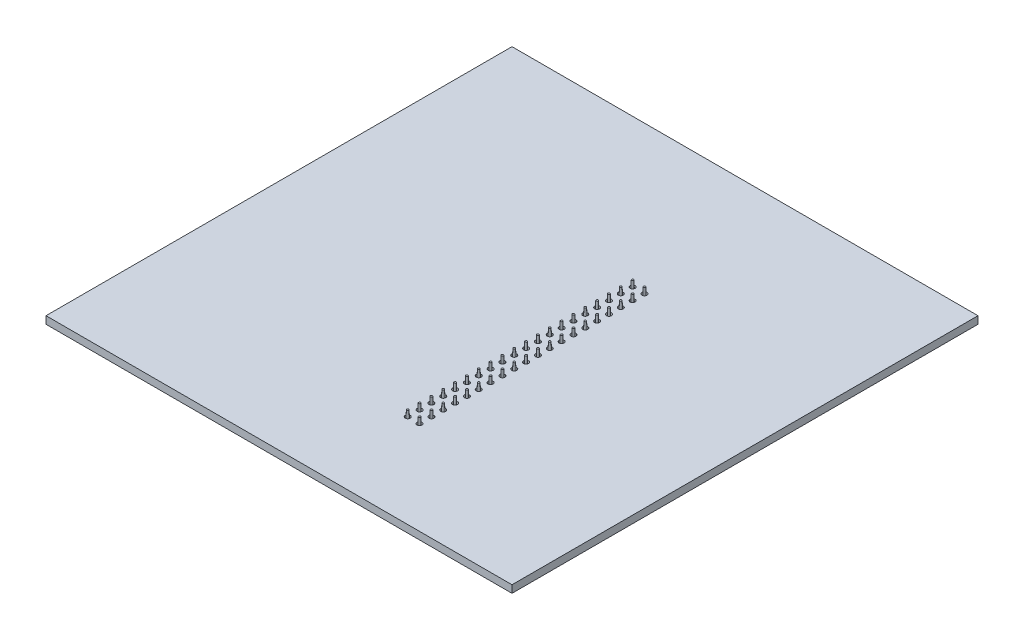
SolidWorks part; units mm, degrees
ref_plane "Front Plane" through (0, 0, 0) normal (0, 0, 1) x (1, 0, 0)
ref_plane "Top Plane" through (0, 0, 0) normal (0, 1, 0) x (1, 0, 0)
ref_plane "Right Plane" through (0, 0, 0) normal (1, 0, 0) x (0, 0, -1)
sketch "Sketch1" plane through (0, 0, 0) normal (0, 1, 0) x (1, 0, 0)
  line L1 (-50, -50) -> (50, -50)
  line L2 (-50, -50) -> (-50, 50)
  line L3 (-50, 50) -> (50, 50)
  line L4 (50, -50) -> (50, 50)
  line L5 (-50, -50) -> (50, 50) construction
  line L6 (-50, 50) -> (50, -50) construction
  point P0 (0, 0)
  dimension "D1" = 100
  dimension "D2" = 100
extrude "Boss-Extrude1" add sketch "Sketch1" along normal blind 1.6
sketch "Sketch2" plane through (0, 1.6, 0) normal (0, 1, 0) x (1, 0, 0)
  line L0 (10.138, -29.974) -> (10.138, -27.434) construction
  circle A0 centre (10.138, -29.974) radius 0.535
  circle A1 centre (7.598, -29.974) radius 0.535
  circle A2 centre (7.598, -27.434) radius 0.535
  circle A3 centre (7.598, -24.894) radius 0.535
  circle A4 centre (7.598, -22.354) radius 0.535
  circle A5 centre (7.598, -19.814) radius 0.535
  circle A6 centre (7.598, -17.274) radius 0.535
  circle A7 centre (7.598, -14.734) radius 0.535
  circle A8 centre (7.598, -12.194) radius 0.535
  circle A9 centre (7.598, -9.654) radius 0.535
  circle A10 centre (7.598, -7.114) radius 0.535
  circle A11 centre (7.598, -4.574) radius 0.535
  circle A12 centre (7.598, -2.034) radius 0.535
  circle A13 centre (7.598, 0.506) radius 0.535
  circle A14 centre (7.598, 3.046) radius 0.535
  circle A15 centre (7.598, 5.586) radius 0.535
  circle A16 centre (7.598, 8.126) radius 0.535
  circle A17 centre (7.598, 10.666) radius 0.535
  circle A18 centre (7.598, 13.206) radius 0.535
  circle A19 centre (7.598, 15.746) radius 0.535
  circle A20 centre (7.598, 18.286) radius 0.535
  circle A21 centre (10.138, -27.434) radius 0.535
  circle A22 centre (10.138, -24.894) radius 0.535
  circle A23 centre (10.138, -22.354) radius 0.535
  circle A24 centre (10.138, -19.814) radius 0.535
  circle A25 centre (10.138, -17.274) radius 0.535
  circle A26 centre (10.138, -14.734) radius 0.535
  circle A27 centre (10.138, -12.194) radius 0.535
  circle A28 centre (10.138, -9.654) radius 0.535
  circle A29 centre (10.138, -7.114) radius 0.535
  circle A30 centre (10.138, -4.574) radius 0.535
  circle A31 centre (10.138, -2.034) radius 0.535
  circle A32 centre (10.138, 0.506) radius 0.535
  circle A33 centre (10.138, 3.046) radius 0.535
  circle A34 centre (10.138, 5.586) radius 0.535
  circle A35 centre (10.138, 8.126) radius 0.535
  circle A36 centre (10.138, 10.666) radius 0.535
  circle A37 centre (10.138, 13.206) radius 0.535
  circle A38 centre (10.138, 15.746) radius 0.535
  circle A39 centre (10.138, 18.286) radius 0.535
  dimension "D1" = 1.07
  dimension "D2" = 39.862
  dimension "D3" = 20.026
  dimension "D6" = 2.54
  dimension "D4" = 2
  dimension "D5" = 20
extrude "Cut-Extrude1" cut sketch "Sketch2" against normal through all
ref_plane "Plane1" through (0, -9.4, 0) normal (0, -1, 0) x (-1, 0, 0)
sketch "Sketch4" plane through (0, -9.4, 0) normal (0, 1, 0) x (1, 0, 0)
  line L0 (9.368, -29.204) -> (10.908, -29.204)
  line L1 (8.868, -31.244) -> (11.408, -31.244)
  line L2 (8.868, -31.244) -> (8.868, -28.704)
  line L3 (8.868, -28.704) -> (11.408, -28.704)
  line L4 (11.408, -31.244) -> (11.408, -28.704)
  line L5 (8.868, -31.244) -> (11.408, -28.704) construction
  line L6 (8.868, -28.704) -> (11.408, -31.244) construction
  line L7 (10.908, -30.744) -> (10.908, -29.204)
  line L8 (9.368, -30.744) -> (10.908, -30.744)
  line L9 (9.368, -30.744) -> (9.368, -29.204)
  point P0 (10.138, -29.974)
  dimension "D1" = 2.54
  dimension "D2" = 2.54
  dimension "D3" = 0.5
extrude "Boss-Extrude2" add sketch "Sketch4" against normal blind 8.4
pattern_linear "LPattern2" count 20 spacing 2.54 along (0, 0, -1) count 2 spacing 2.54 along (-1, 0, 0) of "Boss-Extrude2"
sketch "Sketch5" plane through (0, -9.4, 0) normal (0, -1, 0) x (-1, 0, 0)
  circle A0 centre (-7.598, 3.046) radius 0.535 construction
  circle A1 centre (-7.598, 5.586) radius 0.535 construction
  circle A2 centre (-7.598, 8.126) radius 0.535 construction
  circle A3 centre (-7.598, 10.666) radius 0.535 construction
  circle A4 centre (-7.598, 13.206) radius 0.535 construction
  circle A5 centre (-7.598, 15.746) radius 0.535 construction
  circle A6 centre (-7.598, 18.286) radius 0.535 construction
  circle A7 centre (-10.138, 18.286) radius 0.535 construction
  circle A8 centre (-10.138, 15.746) radius 0.535 construction
  circle A9 centre (-10.138, 13.206) radius 0.535 construction
  circle A10 centre (-10.138, 10.666) radius 0.535 construction
  circle A11 centre (-10.138, 8.126) radius 0.535 construction
  circle A12 centre (-10.138, 5.586) radius 0.535 construction
  circle A13 centre (-10.138, 3.046) radius 0.535 construction
  circle A14 centre (-7.598, 0.506) radius 0.535 construction
  circle A15 centre (-10.138, 0.506) radius 0.535 construction
  circle A16 centre (-10.138, -2.034) radius 0.535 construction
  circle A17 centre (-7.598, -2.034) radius 0.535 construction
  circle A18 centre (-7.598, -4.574) radius 0.535 construction
  circle A19 centre (-10.138, -4.574) radius 0.535 construction
  circle A20 centre (-10.138, -7.114) radius 0.535 construction
  circle A21 centre (-7.598, -7.114) radius 0.535 construction
  circle A22 centre (-7.598, -9.654) radius 0.535 construction
  circle A23 centre (-10.138, -9.654) radius 0.535 construction
  circle A24 centre (-7.598, -12.194) radius 0.535 construction
  circle A25 centre (-10.138, -12.194) radius 0.535 construction
  circle A26 centre (-10.138, -14.734) radius 0.535 construction
  circle A27 centre (-7.598, -14.734) radius 0.535 construction
  circle A28 centre (-7.598, -17.274) radius 0.535 construction
  circle A29 centre (-10.138, -17.274) radius 0.535 construction
  circle A30 centre (-10.138, -19.814) radius 0.535 construction
  circle A31 centre (-7.598, -19.814) radius 0.535 construction
  circle A32 centre (-7.598, -22.354) radius 0.535 construction
  circle A33 centre (-10.138, -22.354) radius 0.535 construction
  circle A34 centre (-7.598, -24.894) radius 0.535 construction
  circle A35 centre (-10.138, -24.894) radius 0.535 construction
  circle A36 centre (-7.598, -27.434) radius 0.535 construction
  circle A37 centre (-10.138, -27.434) radius 0.535 construction
  circle A38 centre (-10.138, -29.974) radius 0.535 construction
  circle A39 centre (-7.598, -29.974) radius 0.535 construction
  circle A40 centre (-7.598, 3.046) radius 0.535
  circle A41 centre (-7.598, 5.586) radius 0.535
  circle A42 centre (-7.598, 8.126) radius 0.535
  circle A43 centre (-7.598, 10.666) radius 0.535
  circle A44 centre (-7.598, 13.206) radius 0.535
  circle A45 centre (-7.598, 15.746) radius 0.535
  circle A46 centre (-7.598, 18.286) radius 0.535
  circle A47 centre (-10.138, 18.286) radius 0.535
  circle A48 centre (-10.138, 15.746) radius 0.535
  circle A49 centre (-10.138, 13.206) radius 0.535
  circle A50 centre (-10.138, 10.666) radius 0.535
  circle A51 centre (-10.138, 8.126) radius 0.535
  circle A52 centre (-10.138, 5.586) radius 0.535
  circle A53 centre (-10.138, 3.046) radius 0.535
  circle A54 centre (-7.598, 0.506) radius 0.535
  circle A55 centre (-10.138, 0.506) radius 0.535
  circle A56 centre (-10.138, -2.034) radius 0.535
  circle A57 centre (-7.598, -2.034) radius 0.535
  circle A58 centre (-7.598, -4.574) radius 0.535
  circle A59 centre (-10.138, -4.574) radius 0.535
  circle A60 centre (-10.138, -7.114) radius 0.535
  circle A61 centre (-7.598, -7.114) radius 0.535
  circle A62 centre (-7.598, -9.654) radius 0.535
  circle A63 centre (-10.138, -9.654) radius 0.535
  circle A64 centre (-7.598, -12.194) radius 0.535
  circle A65 centre (-10.138, -12.194) radius 0.535
  circle A66 centre (-10.138, -14.734) radius 0.535
  circle A67 centre (-7.598, -14.734) radius 0.535
  circle A68 centre (-7.598, -17.274) radius 0.535
  circle A69 centre (-10.138, -17.274) radius 0.535
  circle A70 centre (-10.138, -19.814) radius 0.535
  circle A71 centre (-7.598, -19.814) radius 0.535
  circle A72 centre (-7.598, -22.354) radius 0.535
  circle A73 centre (-10.138, -22.354) radius 0.535
  circle A74 centre (-7.598, -24.894) radius 0.535
  circle A75 centre (-10.138, -24.894) radius 0.535
  circle A76 centre (-7.598, -27.434) radius 0.535
  circle A77 centre (-10.138, -27.434) radius 0.535
  circle A78 centre (-10.138, -29.974) radius 0.535
  circle A79 centre (-7.598, -29.974) radius 0.535
extrude "Boss-Extrude3" add sketch "Sketch5" against normal blind 12.3 draft 1.5 separate body
